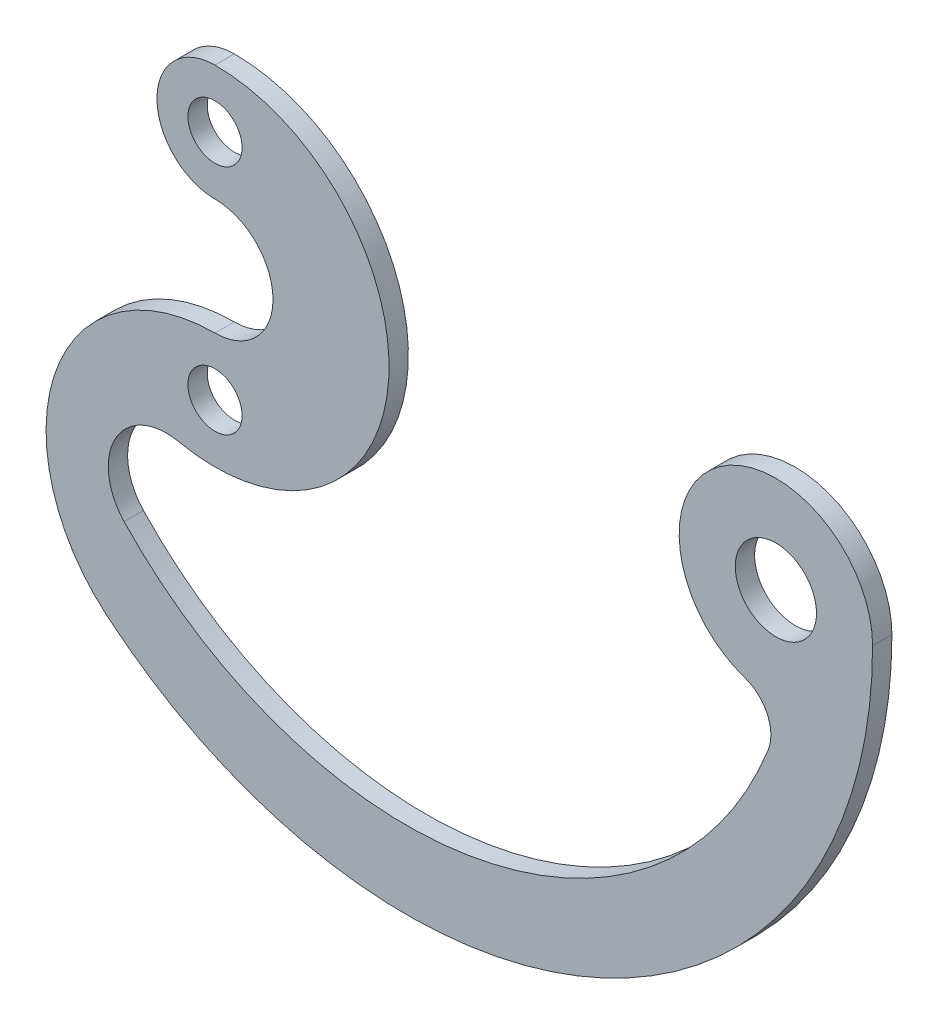
SolidWorks part; units mm, degrees
material "Thornel Mat VMA"
ref_plane "前视基准面" through (0, 0, 0) normal (0, 0, 1) x (1, 0, 0)
ref_plane "上视基准面" through (0, 0, 0) normal (0, 1, 0) x (1, 0, 0)
ref_plane "右视基准面" through (0, 0, 0) normal (1, 0, 0) x (0, 0, -1)
sketch "草图1" plane through (0, 0, 0) normal (0, 0, 1) x (1, 0, 0)
  line L0 (0, 0) -> (29, 0) construction
  arc A0 (0, -3) -> (0, 3) centre (0, 0) ccw
  circle A1 centre (0, 0) radius 6 construction
  circle A2 centre (0, 6) radius 1.4
  circle A3 centre (0, -6) radius 1.4
  circle A4 centre (29, 0) radius 2.1
  arc A5 (0, 9) -> (0, 3) centre (0, 6) ccw
  arc A7 (34, 0) -> (27.3877, -4.7329) centre (29, 0) ccw
  arc A8 (-1.8881, -8.7997) -> (0, 9) centre (0, 0) ccw
  arc A14 (0, -3) -> (-5.6348, -18.4048) centre (0, -11.733) ccw
  arc A16 (-5.6348, -18.4048) -> (34, 0) centre (9.9094, 0) ccw
  arc A17 (-4.6988, -13.7925) -> (28.6039, -7.3586) centre (9.9094, 0) ccw
  arc A18 (-1.8881, -8.7997) -> (-4.6988, -13.7925) centre (-2.5175, -11.733) ccw
  arc A19 (27.3877, -4.7329) -> (28.6039, -7.3586) centre (26.7428, -6.6261) cw
  dimension "D1" = 6
  dimension "D2" = 12
  dimension "D3" = 2.8
  dimension "D5" = 4.2
  dimension "D6" = 10
  dimension "D7" = 3
  dimension "D8" = 2
  dimension "D9" = 4
  dimension "D4" = 29
extrude "凸台-拉伸1" add sketch "草图1" along normal blind 1
